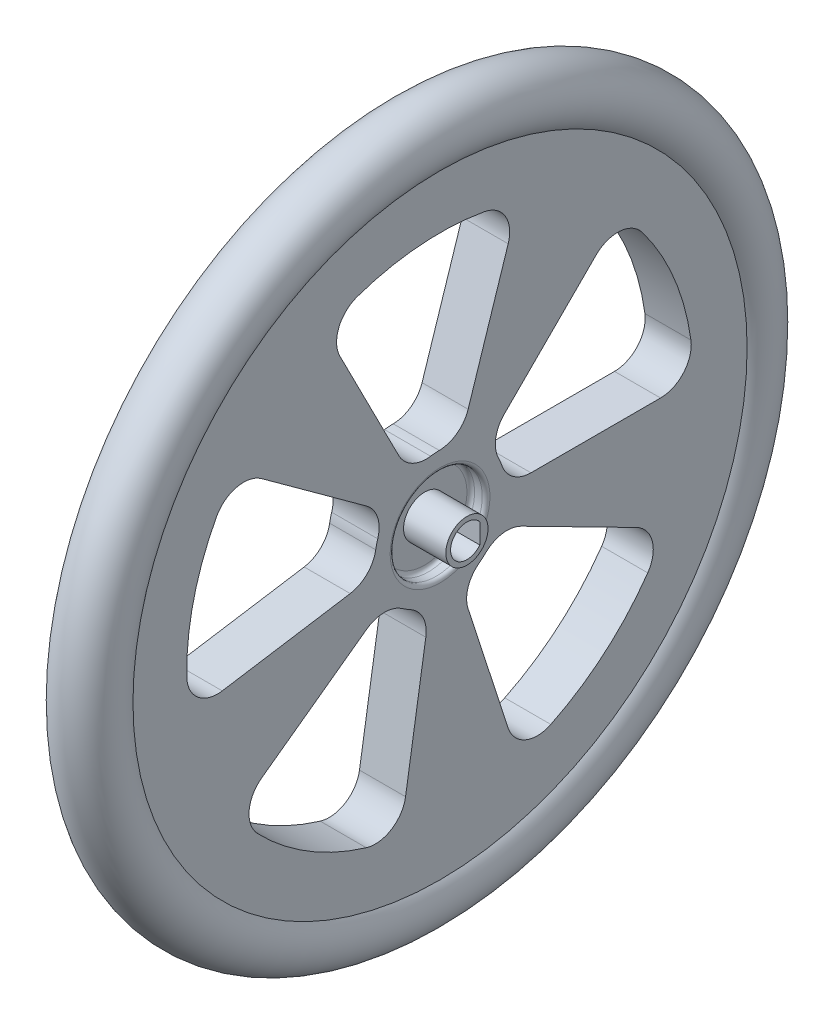
SolidWorks part; units mm, degrees
material "ABS"
ref_plane "Front Plane" through (0, 0, 0) normal (0, 0, 1) x (1, 0, 0)
ref_plane "Top Plane" through (0, 0, 0) normal (0, 1, 0) x (1, 0, 0)
ref_plane "Right Plane" through (0, 0, 0) normal (1, 0, 0) x (0, 0, -1)
sketch "Sketch3" plane through (0, 0, 0) normal (0, 0, 1) x (1, 0, 0)
  line L0 (0, 0) -> (10.5995, 0) construction
  line L1 (0, 0) -> (0, 40) construction
  line L2 (-1, 0) -> (1, 0)
  line L3 (1, 0) -> (1, 5.5)
  line L4 (1.5, 6) -> (2.5, 6)
  line L5 (3, 6.5) -> (3, 40)
  line L6 (-3, 6.5) -> (-3, 40)
  line L7 (-1.5, 6) -> (-2.5, 6)
  line L8 (-1, 0) -> (-1, 5.5)
  line L10 (3, 40) -> (-3, 40) construction
  line L11 (-4, 42.6458) -> (4, 42.6458) construction
  arc A0 (1, 5.5) -> (1.5, 6) centre (1.5, 5.5) cw
  arc A1 (2.5, 6) -> (3, 6.5) centre (2.5, 6.5) ccw
  arc A4 (-2.5, 6) -> (-3, 6.5) centre (-2.5, 6.5) cw
  arc A5 (-1, 5.5) -> (-1.5, 6) centre (-1.5, 5.5) ccw
  arc A7 (3, 40) -> (-3, 40) centre (0, 42.6458) ccw
  point P3 (-1, 0)
  point P12 (1, 6)
  point P15 (3, 6)
  point P18 (1, 0)
  point P29 (0, 0)
  point P30 (-3, 6)
  point P31 (-1, 6)
  dimension "D6" = 0.5
  dimension "D1" = 3
  dimension "D2" = 0
  dimension "D3" = 6
  dimension "D4" = 2
  dimension "D5" = 40
  dimension "D7" = 8
revolve "Shape_Roue" add sketch "Sketch3" angle 360 about L0
sketch "Sketch6" plane through (3, 0, 0) normal (1, 0, 0) x (0, 0, -1)
  line L0 (8.3741, 8.3741) -> (20.3101, 20.3101)
  line L1 (28.7228, 0) -> (11.8427, 0)
  line L2 (0, 0) -> (24.1309, 0) construction
  line L3 (0, 0) -> (0, 5.2799) construction
  line L4 (33, 0) -> (0, 0) construction
  line L5 (23.3345, 23.3345) -> (0, 0) construction
  circle A0 centre (0, 0) radius 6.5 construction
  arc A1 (8.3741, 8.3741) -> (7.6177, 3.771) centre (11.2025, 5.5456) ccw
  arc A2 (7.6177, 3.771) -> (8.053, 2.72) centre (0, 0) cw
  arc A3 (26.33, 19.8929) -> (32.6846, 4.5517) centre (0, 0) cw
  arc A5 (11.8427, 0) -> (8.053, 2.72) centre (11.8427, 4) cw
  arc A6 (28.7228, 0) -> (32.6846, 4.5517) centre (28.7228, 4) ccw
  arc A7 (20.3101, 20.3101) -> (26.33, 19.8929) centre (23.1385, 17.4817) cw
  circle A8 centre (0, 0) radius 40 construction
  dimension "D1" = 45
  dimension "D3" = 2
  dimension "D5" = 4
  dimension "D2" = 7
extrude "Cut-Extrude1" cut sketch "Sketch6" against normal up to next (6 mm away)
pattern_circular "CirPattern1" count 5 over 360 about axis through (0, 0, 0) along (1, 0, 0) of "Cut-Extrude1"
sketch "Sketch7" plane through (-1, 0, 0) normal (1, 0, 0) x (0, 0, -1)
  line L0 (0, 0) -> (1.9231, 0) construction
  line L1 (0, -2.125) -> (0, 2.125) construction
  line L2 (0, 0) -> (-2.125, 0)
  line L3 (1.675, 1.3077) -> (1.675, -1.3077)
  arc A0 (1.675, 1.3077) -> (1.675, -1.3077) centre (0, 0) ccw
  dimension "D1" = 4.25
  dimension "D2" = 3.8
sketch "Sketch8" plane through (1, 0, 0) normal (1, 0, 0) x (0, 0, -1)
  line L0 (0, 0) -> (2.75, 0) construction
  circle A0 centre (0, 0) radius 2.75
  dimension "D1" = 2.75
extrude "Boss-Extrude1" add sketch "Sketch8" along normal blind 5.5
extrude "Cut-Extrude2" cut sketch "Sketch7" along normal up to next
